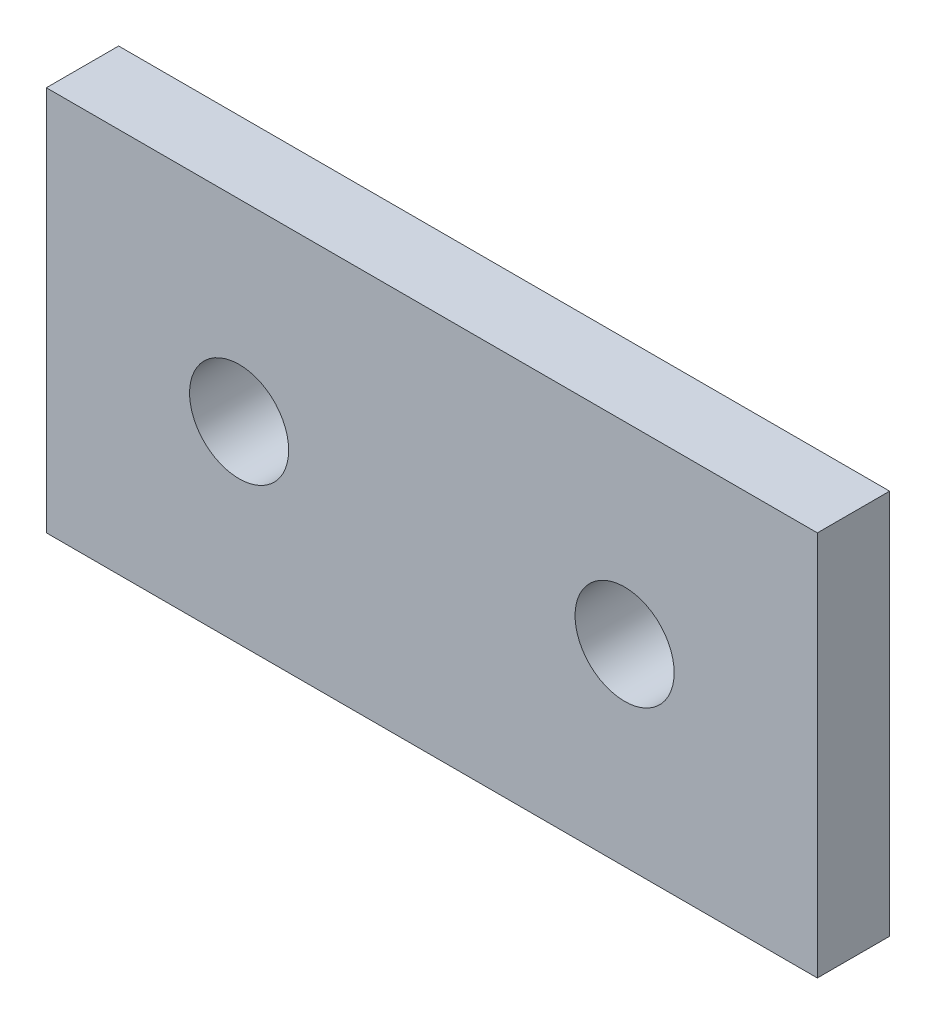
SolidWorks part; units mm, degrees
ref_plane "Front Plane" through (0, 0, 0) normal (0, 0, 1) x (1, 0, 0)
ref_plane "Top Plane" through (0, 0, 0) normal (0, 1, 0) x (1, 0, 0)
ref_plane "Right Plane" through (0, 0, 0) normal (1, 0, 0) x (0, 0, -1)
sketch "Sketch1" plane through (0, 0, 0) normal (0, 0, 1) x (1, 0, 0)
  line L0 (0, 0) -> (0, 25.4)
  line L1 (12.7, 12.7) -> (38.1, 12.7) construction
  line L4 (50.8, 25.4) -> (0, 25.4)
  line L5 (50.8, 0) -> (0, 0)
  line L7 (50.8, 25.4) -> (50.8, 0)
  circle A0 centre (12.7, 12.7) radius 3.2639
  circle A1 centre (38.1, 12.7) radius 3.2639
  dimension "D1" = 25.4
  dimension "E" = 6.5278
  dimension "D2" = 12.7
  dimension "C" = 25.4
  dimension "D3" = 12.7
  dimension "B" = 50.8
extrude "Boss-Extrude1" add sketch "Sketch1" along normal mid plane 4.7625
